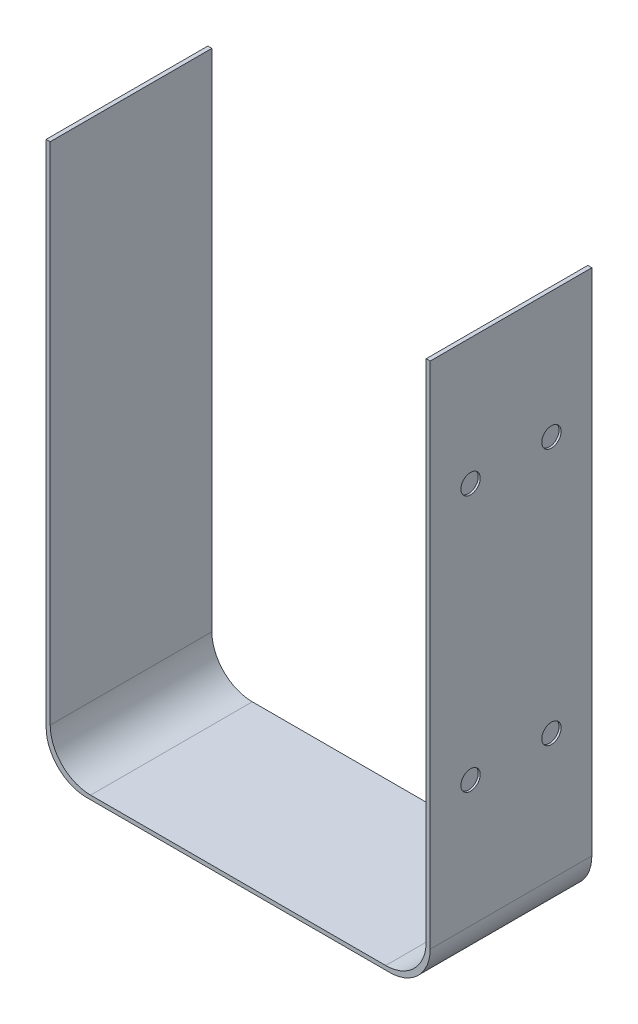
SolidWorks part; units mm, degrees
material "Nikiel"
ref_plane "Płaszczyzna przednia" through (0, 0, 0) normal (0, 0, 1) x (1, 0, 0)
ref_plane "Płaszczyzna górna" through (0, 0, 0) normal (0, 1, 0) x (1, 0, 0)
ref_plane "Płaszczyzna prawa" through (0, 0, 0) normal (1, 0, 0) x (0, 0, -1)
sketch "Szkic1" plane through (0, 0, 0) normal (0, 0, 1) x (1, 0, 0)
  line L5 (-56.6516, 21.7786) -> (-56.8516, 21.7786)
  line L9 (-37.8516, 21.7786) -> (-38.0516, 21.7786)
  line L25 (-56.6516, 21.7786) -> (-56.6516, -3.2214)
  line L26 (-56.8516, 21.7786) -> (-56.8516, -3.4214)
  line L29 (-38.0516, 21.7786) -> (-38.0516, -3.2214)
  line L30 (-37.8516, 21.7786) -> (-37.8516, -3.4214)
  line L31 (-54.8516, -5.4214) -> (-39.8516, -5.4214)
  line L32 (-54.6516, -5.2214) -> (-40.0516, -5.2214)
  arc A13 (-56.6516, -3.2214) -> (-54.6516, -5.2214) centre (-54.6516, -3.2214) ccw
  arc A14 (-56.8516, -3.4214) -> (-54.8516, -5.4214) centre (-54.8516, -3.4214) ccw
  arc A15 (-38.0516, -3.2214) -> (-40.0516, -5.2214) centre (-40.0516, -3.2214) cw
  arc A16 (-37.8516, -3.4214) -> (-39.8516, -5.4214) centre (-39.8516, -3.4214) cw
  dimension "D2" = 2
  dimension "D3" = 2
  dimension "D4" = 2
  dimension "D5" = 2
  dimension "D9" = 0.2
  dimension "D10" = 0.2
extrude "Dodanie-wyciągnięcie1" add sketch "Szkic1" along normal blind 8
sketch "Szkic2" plane through (-37.8516, 0, 0) normal (1, 0, 0) x (0, 0, -1)
  circle A0 centre (-6, 15.5286) radius 0.4788
  circle A1 centre (-2, 15.5286) radius 0.4788
  circle A2 centre (-2, 2.8286) radius 0.4788
  circle A3 centre (-6, 2.8286) radius 0.4788
extrude "Wytnij-wyciągnięcie1" cut sketch "Szkic2" against normal blind 0.1
sketch "Szkic3" plane through (-56.8516, 0, 0) normal (-1, 0, 0) x (0, 0, 1)
  circle A0 centre (6, 15.5286) radius 0.5
  circle A1 centre (2, 15.5286) radius 0.5
  circle A2 centre (2, 2.8286) radius 0.5
  circle A3 centre (6, 2.8286) radius 0.5
extrude "Wytnij-wyciągnięcie2" cut sketch "Szkic3" against normal blind 0.1
